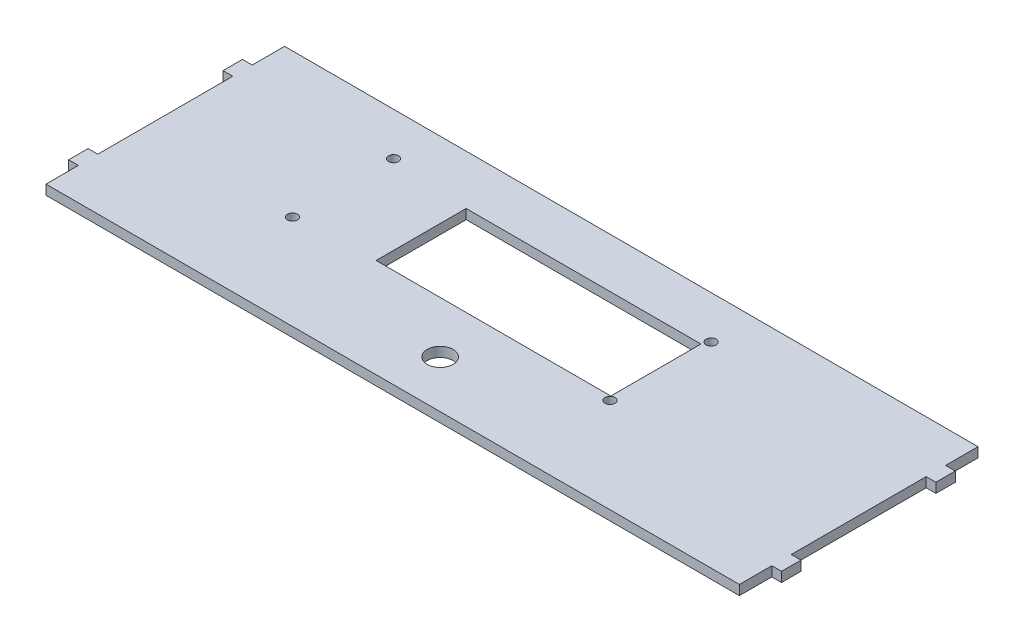
SolidWorks part; units mm, degrees
ref_plane "Alzado" through (0, 0, 0) normal (0, 0, 1) x (1, 0, 0)
ref_plane "Planta" through (0, 0, 0) normal (0, 1, 0) x (1, 0, 0)
ref_plane "Vista lateral" through (0, 0, 0) normal (1, 0, 0) x (0, 0, -1)
sketch "Croquis1" plane through (0, 0, 0) normal (0, 1, 0) x (1, 0, 0)
  line L1 (-107, 36.82) -> (107, 36.82)
  line L2 (-107, 36.82) -> (-107, -36.82)
  line L3 (-107, -36.82) -> (107, -36.82)
  line L4 (107, 36.82) -> (107, -36.82)
  line L5 (-107, 36.82) -> (107, -36.82) construction
  line L6 (-107, -36.82) -> (107, 36.82) construction
  point P0 (0, 0)
  dimension "D1" = 214
  dimension "D2" = 73.64
extrude "Saliente-Extruir1" add sketch "Croquis1" along normal blind 3
sketch "Croquis2" plane through (0, 3, 0) normal (0, 1, 0) x (1, 0, 0)
  line L0 (0, -18.18) -> (0, -26.18) construction
  line L1 (0, 36.82) -> (0, -36.82) construction
  line L8 (107, 36.82) -> (-107, 36.82) construction
  line L10 (-107, -36.82) -> (107, -36.82) construction
  circle A0 centre (0, -22.18) radius 4
  dimension "D1" = 8
  dimension "D2" = 0
  dimension "D5" = 59
sketch "Croquis3" plane through (0, 3, 0) normal (0, 1, 0) x (1, 0, 0)
  line L0 (-107, 36.82) -> (-107, -36.82) construction
  line L1 (-107, 26.82) -> (-110, 26.82)
  line L2 (-107, 26.82) -> (-107, 20.82)
  line L3 (-107, 20.82) -> (-110, 20.82)
  line L4 (-110, 26.82) -> (-110, 20.82)
  line L5 (-107, -36.82) -> (107, -36.82) construction
  line L6 (-107, -26.82) -> (-110, -26.82)
  line L7 (-107, -26.82) -> (-107, -20.82)
  line L8 (-107, -20.82) -> (-110, -20.82)
  line L9 (-110, -26.82) -> (-110, -20.82)
  line L10 (107, 36.82) -> (-107, 36.82) construction
  line L11 (107, -36.82) -> (107, 36.82) construction
  line L12 (107, 26.82) -> (110, 26.82)
  line L13 (107, 26.82) -> (107, 20.82)
  line L14 (107, 20.82) -> (110, 20.82)
  line L15 (110, 26.82) -> (110, 20.82)
  line L17 (107, -20.82) -> (110, -20.82)
  line L18 (107, -20.82) -> (107, -26.82)
  line L19 (107, -26.82) -> (110, -26.82)
  line L20 (110, -20.82) -> (110, -26.82)
  dimension "D1" = 3
  dimension "D2" = 3
  dimension "D3" = 6
  dimension "D4" = 6
  dimension "D5" = 10
  dimension "D6" = 10
  dimension "D7" = 6
  dimension "D8" = 3
  dimension "D9" = 3
  dimension "D10" = 6
  dimension "D11" = 10
  dimension "D12" = 10
extrude "Saliente-Extruir2" add sketch "Croquis3" against normal through all
extrude "Cortar-Extruir1" cut sketch "Croquis2" against normal through all
sketch "Croquis5" plane through (0, 3, 0) normal (0, 1, 0) x (1, 0, 0)
  line L1 (107, 36.82) -> (-107, 36.82) construction
  line L2 (-107, 36.82) -> (-107, 26.82) construction
  line L3 (-107, -36.82) -> (107, -36.82) construction
  line L4 (-107, 20.82) -> (-107, -20.82) construction
  line L6 (107, -20.82) -> (107, 20.82) construction
  line L7 (107, 26.82) -> (107, 36.82) construction
  circle A0 centre (-60.15, 23.605) radius 1.55
  circle A1 centre (37.85, 23.605) radius 1.55
  circle A2 centre (37.85, -7.595) radius 1.55
  circle A3 centre (-60.15, -7.595) radius 1.55
  point P2 (-107, 31.82)
  dimension "D5" = 3.1
  dimension "D6" = 3.1
  dimension "D7" = 3.1
  dimension "D8" = 3.1
  dimension "D1" = 13.215
  dimension "D2" = 46.85
  dimension "D3" = 29.225
  dimension "D4" = 46.85
  dimension "D9" = 29.225
  dimension "D10" = 69.15
  dimension "D11" = 13.215
  dimension "D12" = 69.15
extrude "Cortar-Extruir3" cut sketch "Croquis5" against normal through all
sketch "Croquis6" plane through (0, 3, 0) normal (0, 1, 0) x (1, 0, 0)
  line L0 (37.85, 23.605) -> (37.85, -7.595) construction
  line L1 (-35.65, 21.505) -> (36.8, 21.505)
  line L2 (-35.65, 21.505) -> (-35.65, -6.295)
  line L3 (-35.65, -6.295) -> (36.8, -6.295)
  line L4 (36.8, 21.505) -> (36.8, -6.295)
  line L5 (37.85, -7.595) -> (-60.15, -7.595) construction
  line L6 (-60.15, -7.595) -> (-60.15, 23.605) construction
  line L7 (-60.15, 23.605) -> (37.85, 23.605) construction
  line L8 (-35.65, 7.605) -> (36.8, 7.605) construction
  dimension "D1" = 72.45
  dimension "D2" = 27.8
  dimension "D3" = 15.2
  dimension "D4" = 24.5
extrude "Cortar-Extruir4" cut sketch "Croquis6" against normal through all
